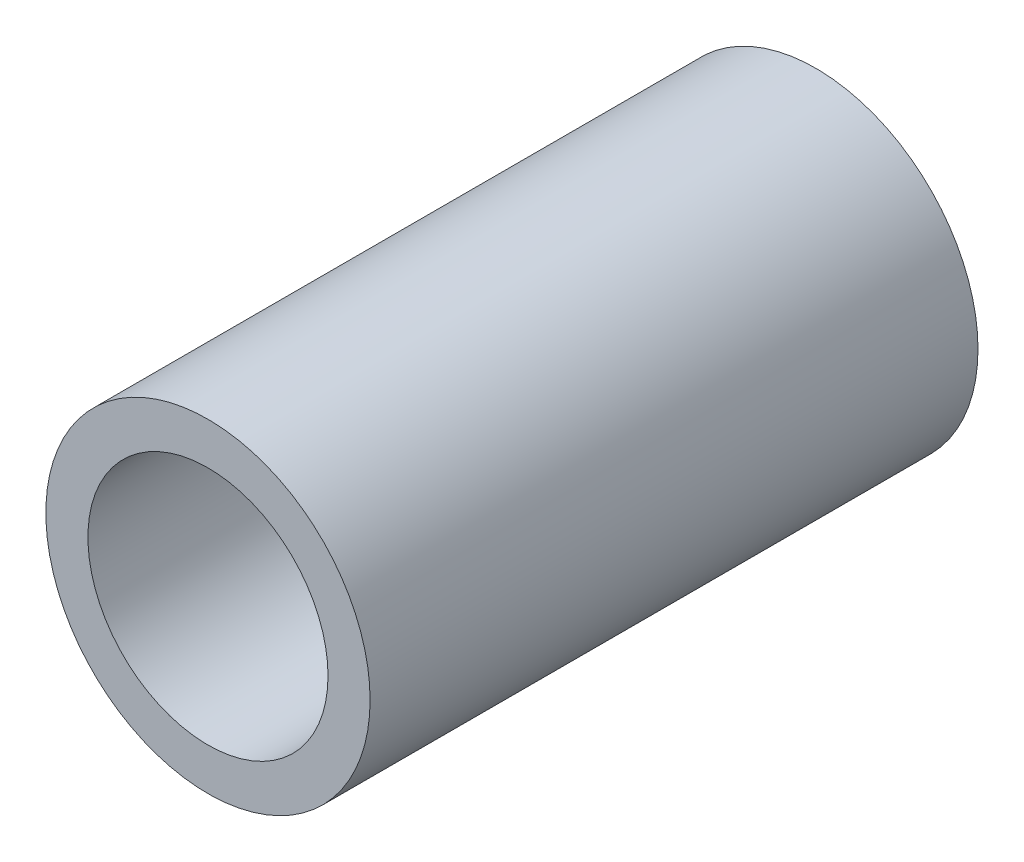
SolidWorks part; units mm, degrees
ref_plane "Front Plane" through (0, 0, 0) normal (0, 0, 1) x (1, 0, 0)
ref_plane "Top Plane" through (0, 0, 0) normal (0, 1, 0) x (1, 0, 0)
ref_plane "Right Plane" through (0, 0, 0) normal (1, 0, 0) x (0, 0, -1)
sketch "Sketch1" plane through (0, 0, 0) normal (0, 0, 1) x (1, 0, 0)
  circle A0 centre (0, 0) radius 10.668
  dimension "Pipe OD" = 21.336
extrude "Extrude-Thin1" add sketch "Sketch1" along normal mid plane 40 thin thin type one direction reverse wall 2.7686
